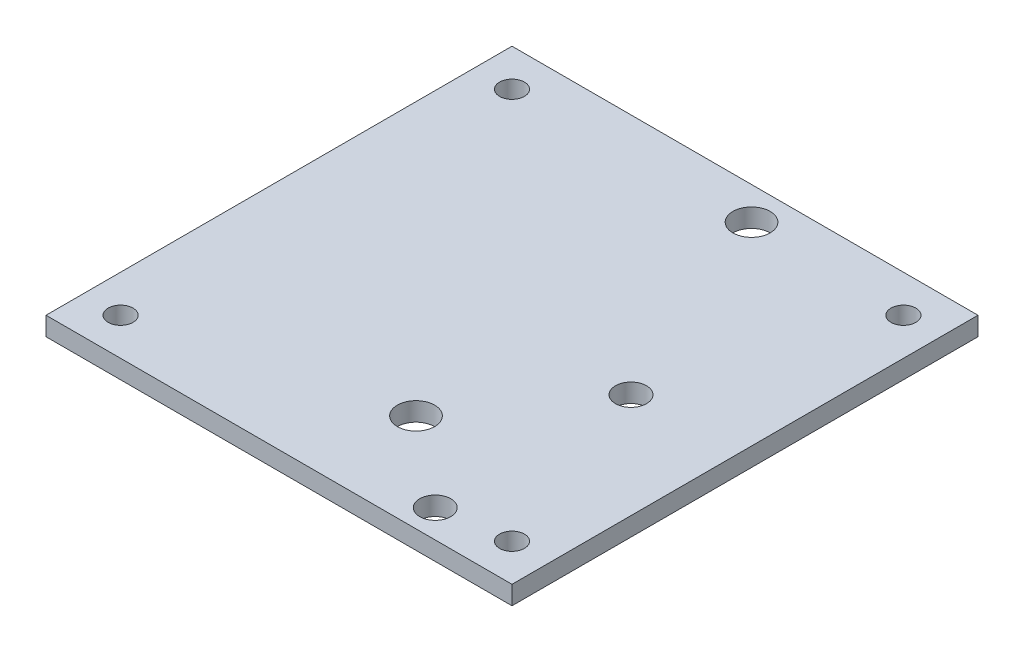
SolidWorks part; units mm, degrees
material "5052-H34"
ref_plane "Front Plane" through (0, 0, 0) normal (0, 0, 1) x (1, 0, 0)
ref_plane "Top Plane" through (0, 0, 0) normal (0, 1, 0) x (1, 0, 0)
ref_plane "Right Plane" through (0, 0, 0) normal (1, 0, 0) x (0, 0, -1)
sketch "Sketch1" plane through (0, 0, 0) normal (0, 1, 0) x (1, 0, 0)
  line L1 (-37.5, -37.5) -> (37.5, -37.5)
  line L2 (-37.5, -37.5) -> (-37.5, 37.5)
  line L3 (-37.5, 37.5) -> (37.5, 37.5)
  line L4 (37.5, -37.5) -> (37.5, 37.5)
  line L5 (-37.5, -37.5) -> (37.5, 37.5) construction
  line L6 (-37.5, 37.5) -> (37.5, -37.5) construction
  circle A0 centre (31.5, 31.5) radius 2
  circle A1 centre (31.5, -31.5) radius 2
  circle A2 centre (-31.5, -31.5) radius 2
  circle A3 centre (-31.5, 31.5) radius 2
  circle A4 centre (20.65, -33) radius 2.5
  circle A5 centre (20.65, -1.5) radius 2.5
  circle A6 centre (6.3, 32.25) radius 3
  circle A7 centre (6.3, -21.75) radius 3
  point P0 (0, 0)
  point P17 (0, 0)
  dimension "D4" = 4
  dimension "D6" = 6
  dimension "D7" = 5
  dimension "D1" = 75
  dimension "D2" = 75
  dimension "D3" = 6
  dimension "D5" = 4
extrude "Boss-Extrude1" add sketch "Sketch1" along normal blind 3
